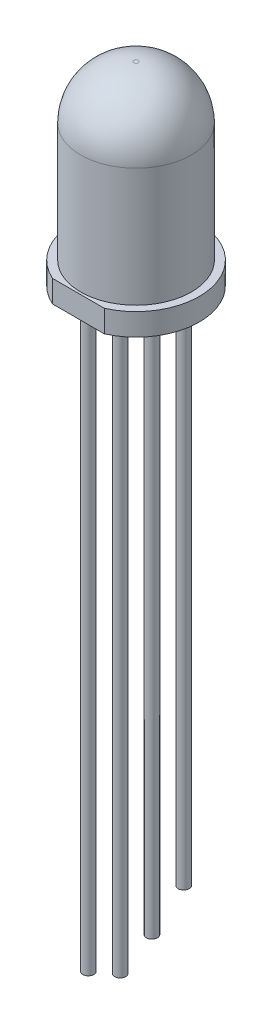
SolidWorks part; units mm, degrees
material "Perspex (TM) GS Acrylic Cast Sheet"
ref_plane "Front Plane" through (0, 0, 0) normal (0, 0, 1) x (1, 0, 0)
ref_plane "Top Plane" through (0, 0, 0) normal (0, 1, 0) x (1, 0, 0)
ref_plane "Right Plane" through (0, 0, 0) normal (1, 0, 0) x (0, 0, -1)
sketch "Sketch1" plane through (0, 0, 0) normal (0, 0, 1) x (1, 0, 0)
  line L0 (0, 0) -> (0, 8.75)
  line L1 (0, 0) -> (2.85, 0)
  line L2 (2.85, 0) -> (2.85, 1)
  line L3 (2.85, 1) -> (2.5, 1)
  line L4 (2.5, 1) -> (2.5, 6.35)
  line L5 (0, 8.75) -> (0.1, 8.75)
  arc A0 (2.5, 6.35) -> (0.1, 8.75) centre (0.1, 6.35) ccw
  dimension "D5" = 0.1
  dimension "D1" = 8.75
  dimension "D2" = 2.85
  dimension "D3" = 2.5
  dimension "D4" = 1
revolve "Revolve1" add sketch "Sketch1" angle 360 about L0
sketch "Sketch2" plane through (0, 0, 0) normal (0, -1, 0) x (1, 0, 0)
  line L0 (0, 0) -> (0, 2.6) construction
  line L1 (-1.1673, 2.6) -> (1.1673, 2.6)
  line L2 (0, 2.6) -> (0, 2.85) construction
  line L3 (0, 0) -> (0, -2.85) construction
  circle A0 centre (0, 0) radius 2.85 construction
  arc A1 (1.1673, 2.6) -> (-1.1673, 2.6) centre (0, 0) ccw
  dimension "D1" = 5.45
extrude "Cut-Extrude1" cut sketch "Sketch2" against normal up to surface (1 mm away) up to face at (0, 1, -2.5)
sketch "Sketch3" plane through (0, 0, 0) normal (0, -1, 0) x (1, 0, 0)
  line L0 (0, 0.7167) -> (0, -0.7167) construction
  line L1 (0, 0.7167) -> (0, 2.15) construction
  line L3 (0, -0.7167) -> (0, -2.15) construction
  circle A0 centre (0, -2.15) radius 0.25
  circle A1 centre (0, 2.15) radius 0.25
  circle A2 centre (0, -0.7167) radius 0.25
  circle A3 centre (0, 0.7167) radius 0.25
  dimension "D2" = 0.5
  dimension "D1" = 4.3
extrude "Boss-Extrude1" add sketch "Sketch3" along normal blind 24.5
sketch "Sketch4" plane through (0, -24.5, 0) normal (0, -1, 0) x (1, 0, 0)
  circle A1 centre (0, 2.15) radius 0.25
  circle A2 centre (0, 2.15) radius 0.25
  circle A3 centre (0, -0.7167) radius 0.25
  circle A4 centre (0, -0.7167) radius 0.25
  dimension "D1" = 0
  dimension "D2" = 0
extrude "Boss-Extrude2" add sketch "Sketch4" along normal offset from surface (1.2 mm away) 25.7 up to face at (0, 0, 0.4667) offset beyond the face yes
sketch "Sketch5" plane through (0, -24.5, 0) normal (0, -1, 0) x (1, 0, 0)
  circle A1 centre (0, 0.7167) radius 0.25
  circle A2 centre (0, 0.7167) radius 0.25
  dimension "D1" = 0
extrude "Boss-Extrude3" add sketch "Sketch5" along normal offset from surface (2 mm away) 26.5 up to face at (0, 0, 0.4667) offset beyond the face yes
